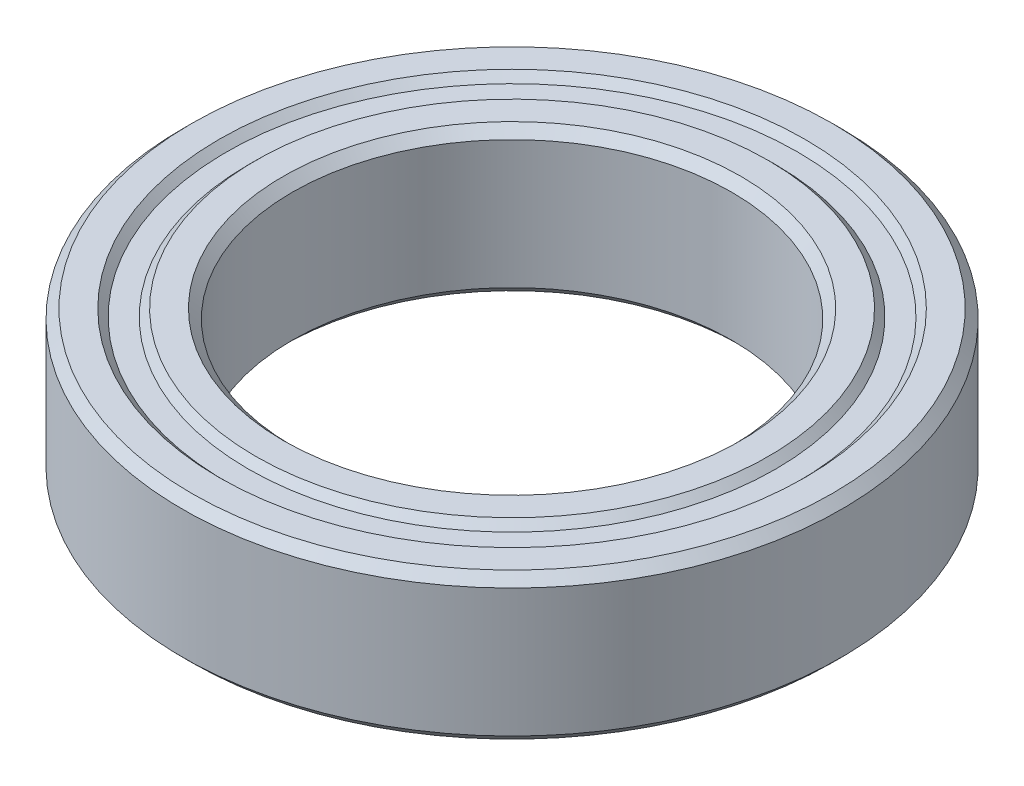
SolidWorks part; units mm, degrees
material "Stainless Steel (ferritic)"
ref_plane "Front Plane" through (0, 0, 0) normal (0, 0, 1) x (1, 0, 0)
ref_plane "Top Plane" through (0, 0, 0) normal (0, 1, 0) x (1, 0, 0)
ref_plane "Right Plane" through (0, 0, 0) normal (1, 0, 0) x (0, 0, -1)
sketch "Sketch1" plane through (0, 0, 0) normal (0, 0, 1) x (1, 0, 0)
  line L0 (0, -1.3494) -> (0, 70.5256) construction
  line L1 (6, 1.75) -> (6, -1.75)
  line L2 (6, -1.75) -> (6.25, -2)
  line L3 (6.25, -2) -> (7, -2)
  line L4 (7, -2) -> (7.2, -1.8)
  line L5 (7.2, -1.8) -> (7.8, -1.8)
  line L6 (7.8, -1.8) -> (8, -2)
  line L7 (8, -2) -> (8.75, -2)
  line L8 (8.75, -2) -> (9, -1.75)
  line L9 (9, -1.75) -> (9, 1.75)
  line L10 (9, 1.75) -> (8.75, 2)
  line L11 (8.75, 2) -> (8, 2)
  line L12 (8, 2) -> (7.8, 1.8)
  line L13 (7.8, 1.8) -> (7.2, 1.8)
  line L14 (7.2, 1.8) -> (7, 2)
  line L15 (7, 2) -> (6.25, 2)
  line L16 (6.25, 2) -> (6, 1.75)
  line L17 (0, 0) -> (6, 0) construction
  dimension "D1" = 6
  dimension "D2" = 4
  dimension "D3" = 0.25
  dimension "D4" = 0.2
  dimension "D5" = 9
  dimension "D6" = 0.75
revolve "Revolve1" add sketch "Sketch1" angle 360 about L0
